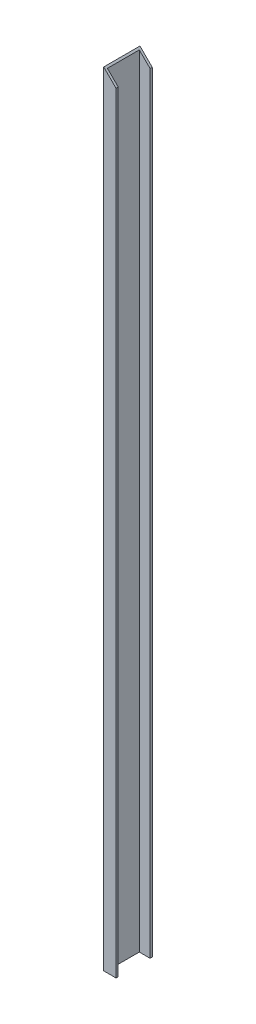
SolidWorks part; units mm, degrees
ref_plane "Front Plane" through (0, 0, 0) normal (0, 0, 1) x (1, 0, 0)
ref_plane "Top Plane" through (0, 0, 0) normal (0, 1, 0) x (1, 0, 0)
ref_plane "Right Plane" through (0, 0, 0) normal (1, 0, 0) x (0, 0, -1)
sketch "Sketch3" plane through (0, 0, 0) normal (0, 1, 0) x (1, 0, 0)
  line L0 (0, 0) -> (43.18, 0)
  line L1 (43.18, 0) -> (43.18, 7.62)
  line L2 (43.18, 7.62) -> (5.3304, 7.62)
  line L3 (5.3304, 7.62) -> (5.3304, 119.38)
  line L4 (5.3304, 119.38) -> (43.18, 119.38)
  line L5 (43.18, 119.38) -> (43.18, 127)
  line L6 (43.18, 127) -> (0, 127)
  line L7 (0, 127) -> (0, 0)
  dimension "D1" = 7.62
  dimension "D2" = 7.62
  dimension "D3" = 127
  dimension "D4" = 43.18
  dimension "D5" = 43.18
extrude "Boss-Extrude2" add sketch "Sketch3" along normal blind 2743.2
sketch "Sketch5" plane through (0, 0, 0) normal (0, 0, 1) x (1, 0, 0)
  line L0 (0, 2743.2) -> (43.18, 2700.02)
  line L1 (43.18, 2743.2) -> (43.18, 0) construction
  line L2 (0, 2743.2) -> (43.18, 2743.2)
  line L3 (43.18, 2743.2) -> (43.18, 2700.02)
extrude "Cut-Extrude1" cut sketch "Sketch5" against normal through all
